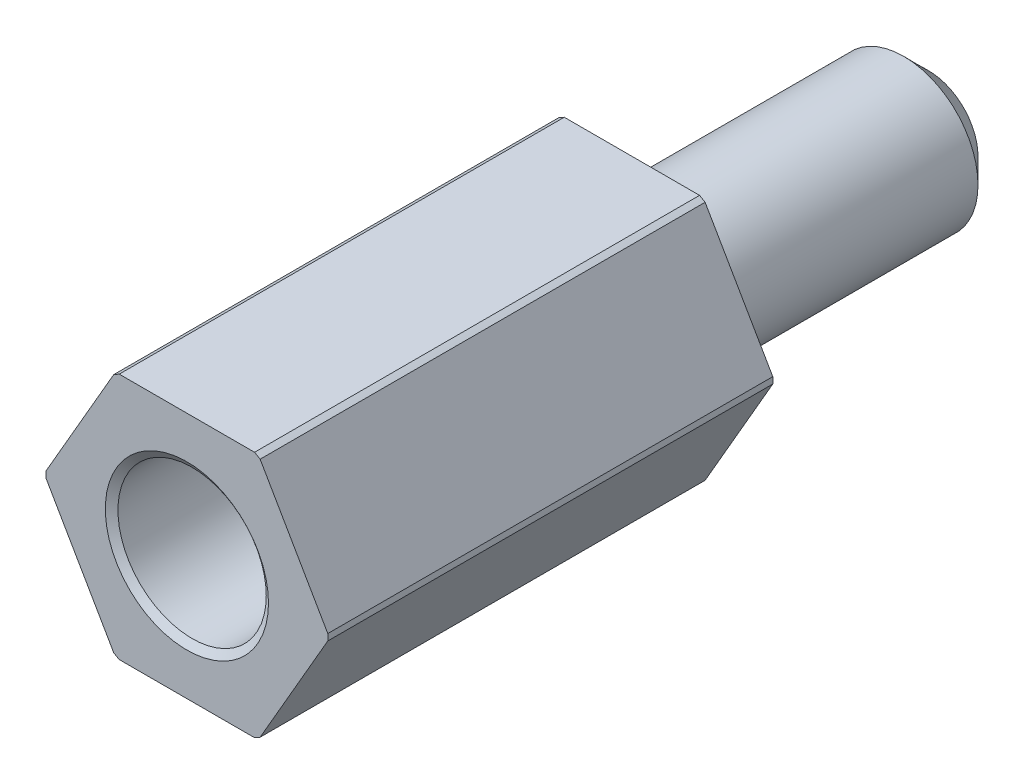
SolidWorks part; units mm, degrees
material "Простая углеродистая сталь"
ref_plane "Front" through (0, 0, 0) normal (0, 0, 1) x (1, 0, 0)
ref_plane "Top" through (0, 0, 0) normal (0, 1, 0) x (1, 0, 0)
ref_plane "Right" through (0, 0, 0) normal (1, 0, 0) x (0, 0, -1)
sketch "Эскиз1" plane through (0, 0, 0) normal (0, 0, 1) x (1, 0, 0)
  line L1 (2.8868, 0) -> (1.4434, 2.5)
  line L2 (1.4434, 2.5) -> (-1.4434, 2.5)
  line L3 (-1.4434, 2.5) -> (-2.8868, 0)
  line L4 (-2.8868, 0) -> (-1.4434, -2.5)
  line L5 (-1.4434, -2.5) -> (1.4434, -2.5)
  line L6 (1.4434, -2.5) -> (2.8868, 0)
  circle A0 centre (0, 0) radius 2.5 construction
  dimension "D1" = 5
extrude "Бобышка-Вытянуть1" add sketch "Эскиз1" along normal blind 15
sketch "Эскиз3" plane through (0, 0, 0) normal (0, 1, 0) x (1, 0, 0)
  line L0 (-1.5, 0) -> (-1.5, -6)
  line L1 (1.4434, 0) -> (-1.4434, 0) construction
  line L2 (-1.5, -6) -> (-2.85, -6)
  line L3 (-2.85, -6) -> (-2.85, -15)
  line L4 (-1.4434, -15) -> (-2.8868, -15) construction
  line L5 (-2.85, -15) -> (-2.8868, -15)
  line L6 (-2.8868, -15) -> (-2.8868, 0)
  line L7 (-2.8868, 0) -> (-1.5, 0)
  line L8 (0, 0) -> (0, -15) construction
  line L9 (1.4434, -15) -> (-1.4434, -15) construction
  dimension "D1" = 3
  dimension "D2" = 5.7
  dimension "D3" = 9
revolve "Вырез-Повернуть1" cut sketch "Эскиз3" angle 360 about L8
cosmetic thread "Условное изображение резьбы1" parameters "D2"=2.439
chamfer "Фаска1" distance 0.5 angle 45 1 edges at (-1.5, 0, 0)
hole_wizard "Отверстие обработанное метчиком M31" positions "Эскиз5" profile "Эскиз4" tap size "M3" standard "DIN"
sketch "Эскиз5" plane through (0, 0, 15) normal (0, 0, 1) x (1, 0, 0)
  point P0 (0, 0)
sketch "Эскиз4" plane through (0, 0, 15) normal (1, 0, 0) x (0, -1, 0)
  line L0 (0, 0) -> (0, 7.7511)
  line L1 (0, 7.7511) -> (1.25, 7)
  line L2 (1.25, 7) -> (1.25, 5)
  line L3 (1.25, 5) -> (1.5, 5)
  line L5 (1.5, 5) -> (1.5, 0.105)
  line L6 (1.5, 0.105) -> (1.65, 0)
  line L7 (1.65, 0) -> (0, 0)
  line L8 (-1.5, 0.105) -> (-1.65, 0) construction
  line L10 (0, 7.7511) -> (-1.25, 7) construction
  line L11 (0, -6.35) -> (0, 107.95) construction
  dimension "Диаметр сверла" = 2.5
  dimension "Глубина сверла" = 7
  dimension "Диаметр резьбы" = 3
  dimension "Глубина резьбы" = 5
  dimension "Диаметр передней зенковки" = 3.3
  dimension "Угол передней зенковки" = 110
  dimension "Угол заточки сверла" = 118
